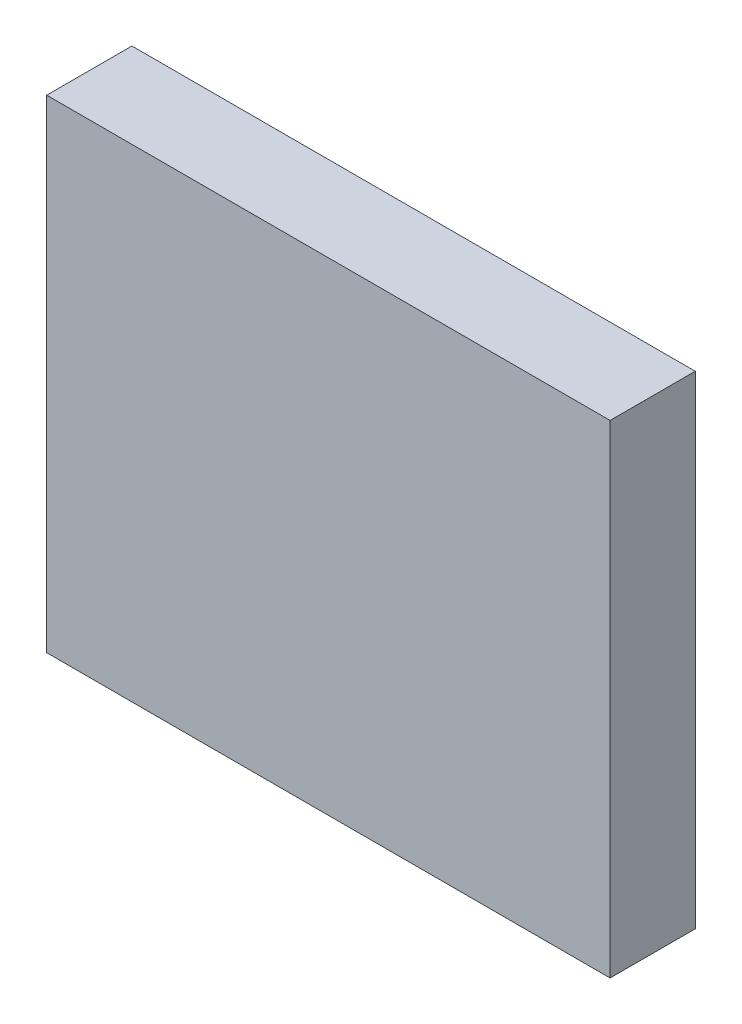
SolidWorks part; units mm, degrees
ref_plane "Front Plane" through (0, 0, 0) normal (0, 0, 1) x (1, 0, 0)
ref_plane "Top Plane" through (0, 0, 0) normal (0, 1, 0) x (1, 0, 0)
ref_plane "Right Plane" through (0, 0, 0) normal (1, 0, 0) x (0, 0, -1)
sketch "Sketch1" plane through (0, 0, 0) normal (0, 0, 1) x (1, 0, 0)
  line L1 (0, 0) -> (21, 0)
  line L2 (0, 0) -> (0, 18)
  line L3 (0, 18) -> (21, 18)
  line L4 (21, 0) -> (21, 18)
extrude "Boss-Extrude1" add sketch "Sketch1" along normal blind 3.175
